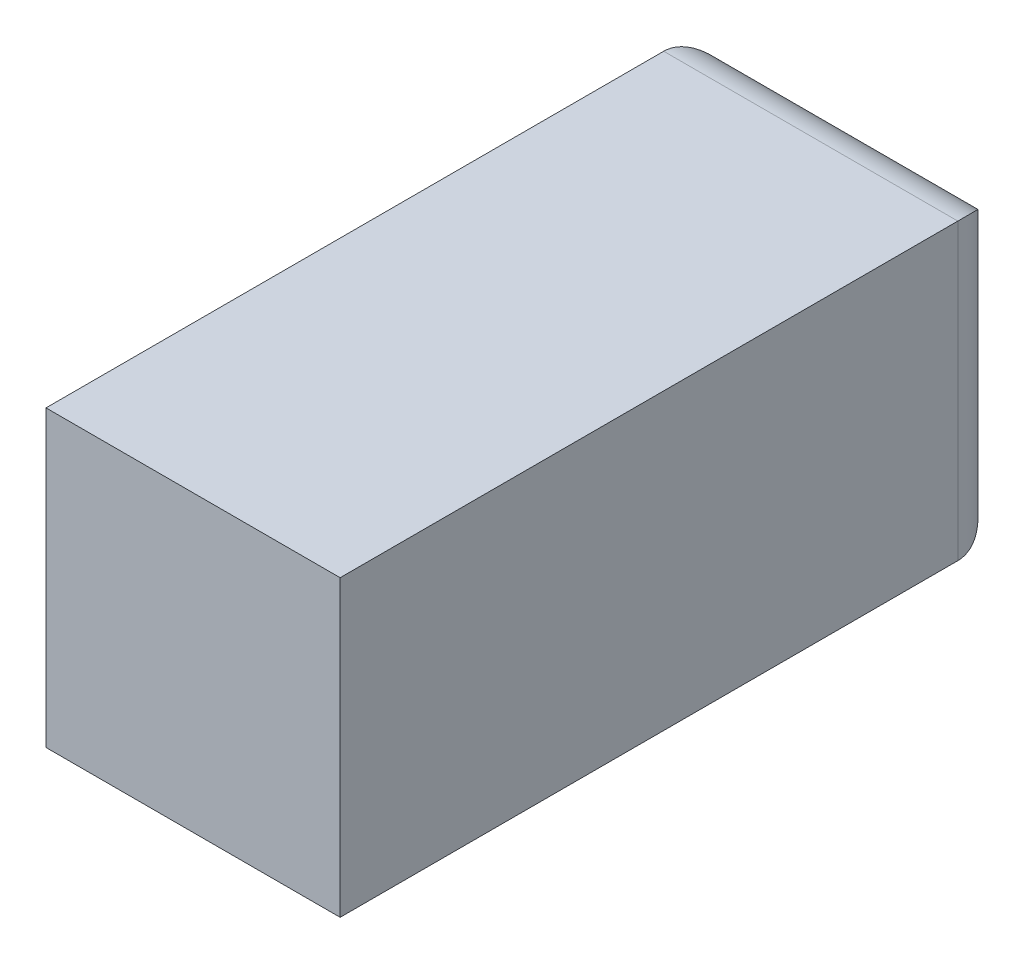
SolidWorks part; units mm, degrees
ref_plane "Front Plane" through (0, 0, 0) normal (0, 0, 1) x (1, 0, 0)
ref_plane "Top Plane" through (0, 0, 0) normal (0, 1, 0) x (1, 0, 0)
ref_plane "Right Plane" through (0, 0, 0) normal (1, 0, 0) x (0, 0, -1)
sketch "Sketch1" plane through (0, 0, 0) normal (0, 0, 1) x (1, 0, 0)
  line L1 (0, 0) -> (15, 0)
  line L2 (0, 0) -> (0, 15)
  line L3 (0, 15) -> (15, 15)
  line L4 (15, 0) -> (15, 15)
  dimension "D1" = 15
  dimension "D2" = 15
extrude "Boss-Extrude1" add sketch "Sketch1" along normal blind 34
fillet "Fillet2" radius 2.5 4 edges at (7.5, 0, 0) (15, 7.5, 0) (7.5, 15, 0) (0, 7.5, 0)
